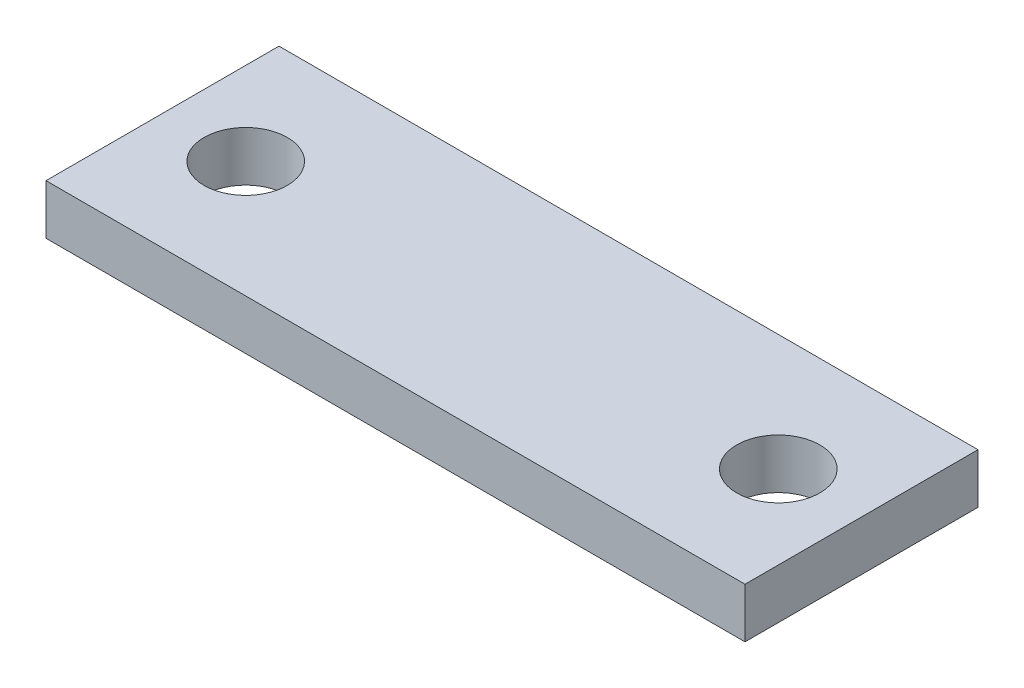
SolidWorks part; units mm, degrees
ref_plane "前视基准面" through (0, 0, 0) normal (0, 0, 1) x (1, 0, 0)
ref_plane "上视基准面" through (0, 0, 0) normal (0, 1, 0) x (1, 0, 0)
ref_plane "右视基准面" through (0, 0, 0) normal (1, 0, 0) x (0, 0, -1)
sketch "草图1" plane through (0, 0, 0) normal (0, 1, 0) x (1, 0, 0)
  line L1 (-21.44, 12.5333) -> (20.56, 12.5333)
  line L2 (-21.44, 12.5333) -> (-21.44, -1.4667)
  line L3 (-21.44, -1.4667) -> (20.56, -1.4667)
  line L4 (20.56, 12.5333) -> (20.56, -1.4667)
  circle A0 centre (-16.44, 5.5333) radius 2.5
  circle A1 centre (15.56, 5.5333) radius 2.5
  dimension "D3" = 5
  dimension "D4" = 5
  dimension "D1" = 42
  dimension "D2" = 14
extrude "凸台-拉伸1" add sketch "草图1" along normal blind 3
